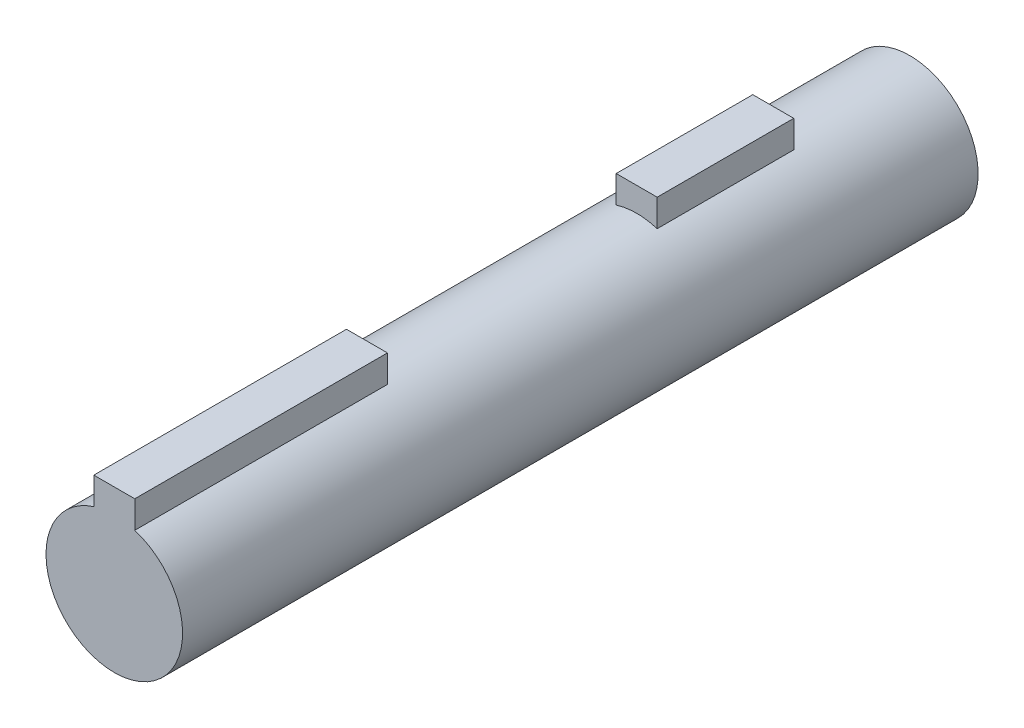
SolidWorks part; units mm, degrees
ref_plane "Front Plane" through (0, 0, 0) normal (0, 0, 1) x (1, 0, 0)
ref_plane "Top Plane" through (0, 0, 0) normal (0, 1, 0) x (1, 0, 0)
ref_plane "Right Plane" through (0, 0, 0) normal (1, 0, 0) x (0, 0, -1)
sketch "Sketch1" plane through (0, 0, 0) normal (0, 0, 1) x (1, 0, 0)
  circle A0 centre (0, 0) radius 5
  dimension "D1" = 10
extrude "Boss-Extrude1" add sketch "Sketch1" along normal blind 20
sketch "Sketch3" plane through (0, 0, 20) normal (0, 0, 1) x (1, 0, 0)
  line L0 (0, 0) -> (0, 7.5667) construction
  line L1 (1.5, 6.7697) -> (-1.5, 6.7697)
  line L2 (1.5, 6.7697) -> (1.5, 4.7697)
  line L3 (-1.5, 6.7697) -> (-1.5, 4.7697)
  circle A1 centre (0, 0) radius 5 construction
  arc A2 (-1.5, 4.7697) -> (1.5, 4.7697) centre (0, 0) ccw
  point P10 (0, 6.7697)
  dimension "D1" = 2
  dimension "D2" = 1.5
extrude "Boss-Extrude2" add sketch "Sketch3" along normal blind 10
sketch "Sketch4" plane through (0, 0, 30) normal (0, 0, 1) x (1, 0, 0)
  circle A0 centre (0, 0) radius 5
extrude "Boss-Extrude3" add sketch "Sketch4" along normal blind 27
sketch "Sketch5" plane through (0, 0, 57) normal (0, 0, 1) x (1, 0, 0)
  line L0 (-1.5, 4.7697) -> (-1.5, 6.7697)
  line L1 (-1.5, 6.7697) -> (1.5, 6.7697)
  line L2 (1.5, 6.7697) -> (1.5, 4.7697)
  arc A0 (-1.5, 4.7697) -> (1.5, 4.7697) centre (0, 0) ccw
extrude "Boss-Extrude4" add sketch "Sketch5" along normal blind 19
sketch "Sketch6" plane through (0, 0, 76) normal (0, 0, 1) x (1, 0, 0)
  circle A0 centre (0, 0) radius 5
extrude "Boss-Extrude5" add sketch "Sketch6" along normal blind 30
sketch "Sketch7" plane through (0, 0, 0) normal (0, 0, -1) x (-1, 0, 0)
  circle A0 centre (0, 0) radius 5
extrude "Cut-Extrude1" cut sketch "Sketch7" against normal blind 10
sketch "Sketch8" plane through (0, 0, 10) normal (0, 0, -1) x (-1, 0, 0)
  circle A0 centre (0, 0) radius 6.9339
extrude "Cut-Extrude2" cut sketch "Sketch8" against normal blind 35
sketch "Sketch9" plane through (0, 0, 45) normal (0, 0, -1) x (-1, 0, 0)
  circle A0 centre (0, 0) radius 5
extrude "Cut-Extrude3" cut sketch "Sketch9" against normal up to surface (12 mm away) up to face at (0, 5.8273, 57)
sketch "Sketch10" plane through (0, 0, 57) normal (0, 0, -1) x (-1, 0, 0)
  circle A0 centre (0, 0) radius 5
extrude "Boss-Extrude8" add sketch "Sketch10" along normal blind 15
sketch "Sketch11" plane through (0, 0, 42) normal (0, 0, -1) x (-1, 0, 0)
  line L0 (-1.5, 6.7697) -> (1.5, 6.7697)
  line L1 (1.5, 6.7697) -> (1.5, 4.7697)
  line L2 (-1.5, 6.7697) -> (-1.5, 4.7697)
  arc A0 (-1.5, 4.7697) -> (1.5, 4.7697) centre (0, 0) ccw
extrude "Boss-Extrude9" add sketch "Sketch11" along normal blind 10
sketch "Sketch12" plane through (0, 0, 32) normal (0, 0, -1) x (-1, 0, 0)
  circle A0 centre (0, 0) radius 5
extrude "Boss-Extrude10" add sketch "Sketch12" along normal blind 10
sketch "Sketch13" plane through (0, 0, 106) normal (0, 0, 1) x (1, 0, 0)
  circle A0 centre (0, 0) radius 5
extrude "Cut-Extrude4" cut sketch "Sketch13" against normal blind 28
sketch "Sketch20" plane through (0, 0, 78) normal (0, 0, 1) x (1, 0, 0)
  circle A0 centre (0, 0) radius 5
extrude "Cut-Extrude5" cut sketch "Sketch20" against normal up to surface (2 mm away) up to face at (0, 5.8273, 76)
sketch "Sketch21" plane through (0, 0, 76) normal (0, 0, 1) x (1, 0, 0)
  line L0 (1.5, 4.7697) -> (1.5, 6.7697) construction
  line L1 (1.5, 6.7697) -> (-1.5, 6.7697) construction
  line L2 (-1.5, 6.7697) -> (-1.5, 4.7697) construction
  line L3 (1.5, 4.7697) -> (1.5, 6.7697)
  line L4 (1.5, 6.7697) -> (-1.5, 6.7697)
  line L5 (-1.5, 6.7697) -> (-1.5, 4.7697)
  arc A0 (-1.5, 4.7697) -> (1.5, 4.7697) centre (0, 0) ccw construction
  arc A1 (-1.5, 4.7697) -> (1.5, 4.7697) centre (0, 0) ccw
extrude "Boss-Extrude11" add sketch "Sketch21" along normal blind 4.25
sketch "Sketch22" plane through (0, 0, 57) normal (0, 0, -1) x (-1, 0, 0)
  line L3 (1.5, 4.7697) -> (1.5, 6.7697)
  line L4 (1.5, 6.7697) -> (-1.5, 6.7697)
  line L5 (-1.5, 6.7697) -> (-1.5, 4.7697)
  line L6 (1.5, 4.7697) -> (1.5, 6.7697)
  line L7 (1.5, 6.7697) -> (-1.5, 6.7697)
  line L8 (-1.5, 6.7697) -> (-1.5, 4.7697)
  arc A1 (1.5, 4.7697) -> (-1.5, 4.7697) centre (0, 0) ccw
  arc A2 (1.5, 4.7697) -> (-1.5, 4.7697) centre (0, 0) ccw
  dimension "D1" = 0
extrude "Cut-Extrude6" cut sketch "Sketch22" against normal blind 22.25
sketch "Sketch23" plane through (0, 0, 79.25) normal (0, 0, -1) x (-1, 0, 0)
  line L3 (1.5, 4.7697) -> (1.5, 6.7697)
  line L4 (1.5, 6.7697) -> (-1.5, 6.7697)
  line L5 (-1.5, 6.7697) -> (-1.5, 4.7697)
  line L6 (1.5, 4.7697) -> (1.5, 6.7697)
  line L7 (1.5, 6.7697) -> (-1.5, 6.7697)
  line L8 (-1.5, 6.7697) -> (-1.5, 4.7697)
  arc A1 (1.5, 4.7697) -> (-1.5, 4.7697) centre (0, 0) ccw
  arc A2 (1.5, 4.7697) -> (-1.5, 4.7697) centre (0, 0) ccw
  dimension "D1" = 0
extrude "Boss-Extrude12" add sketch "Sketch23" along normal blind 17.5
